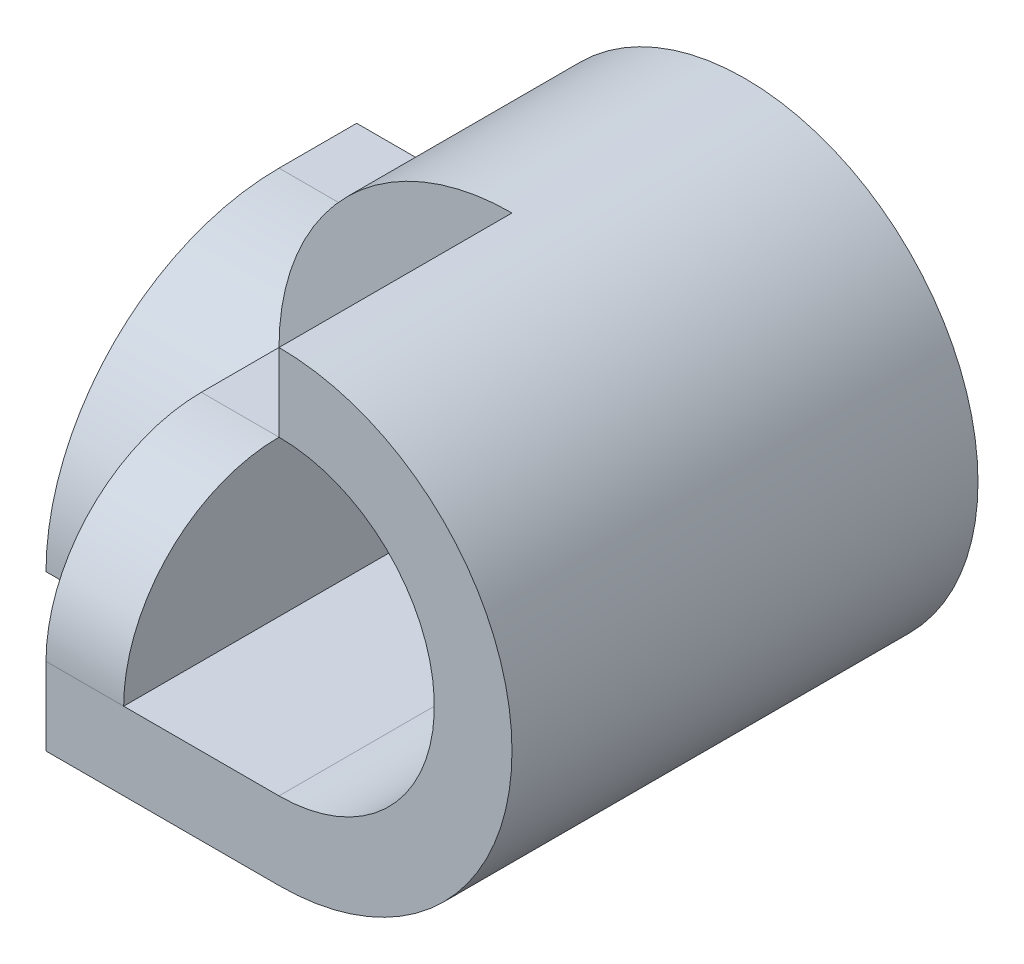
SolidWorks part; units mm, degrees
ref_plane "Front Plane" through (0, 0, 0) normal (0, 0, 1) x (1, 0, 0)
ref_plane "Top Plane" through (0, 0, 0) normal (0, 1, 0) x (1, 0, 0)
ref_plane "Right Plane" through (0, 0, 0) normal (1, 0, 0) x (0, 0, -1)
sketch "Sketch2" plane through (0, 0, 0) normal (0, 0, 1) x (1, 0, 0)
  line L0 (0, 0) -> (0, 2)
  line L1 (0, 0) -> (2, 0)
  line L2 (-1, -1) -> (-1, 2)
  line L3 (-1, -1) -> (2, -1)
  arc A0 (0, 2) -> (2, 0) centre (2, 2) cw
  arc A1 (-1, 2) -> (2, -1) centre (2, 2) cw
  dimension "D2" = 2
  dimension "D1" = 2
  dimension "D3" = 3
  dimension "D4" = 3
extrude "Boss-Extrude1" add sketch "Sketch2" along normal blind 6 contours A1 L2 L3 L0 A0 L1
sketch "Sketch3" plane through (-1, 0, 0) normal (-1, 0, 0) x (0, 0, 1)
  line L0 (0, 2) -> (0, -1)
  line L1 (0, -1) -> (4, -1)
  line L2 (6, -1) -> (0, -1) construction
  line L3 (0, 2) -> (1, 2)
  line L4 (6, 2) -> (0, 2) construction
  arc A0 (1, 2) -> (4, -1) centre (1, -1) cw
  dimension "D1" = 4
  dimension "D2" = 1
extrude "Boss-Extrude2" add sketch "Sketch3" along normal blind 2
sketch "Sketch4" plane through (-1, 0, 0) normal (-1, 0, 0) x (0, 0, 1)
  line L0 (3, 2) -> (4, 2)
  line L1 (6, 2) -> (1, 2) construction
  line L3 (6, 0) -> (6, 5)
  line L4 (6, 5) -> (3, 5)
  line L5 (6, 5) -> (0, 5) construction
  line L6 (3, 5) -> (3, 2)
  arc A0 (4, 2) -> (6, 0) centre (4, 0) cw
  dimension "D1" = 2
  dimension "D2" = 1
extrude "Cut-Extrude1" cut sketch "Sketch4" against normal blind 3
